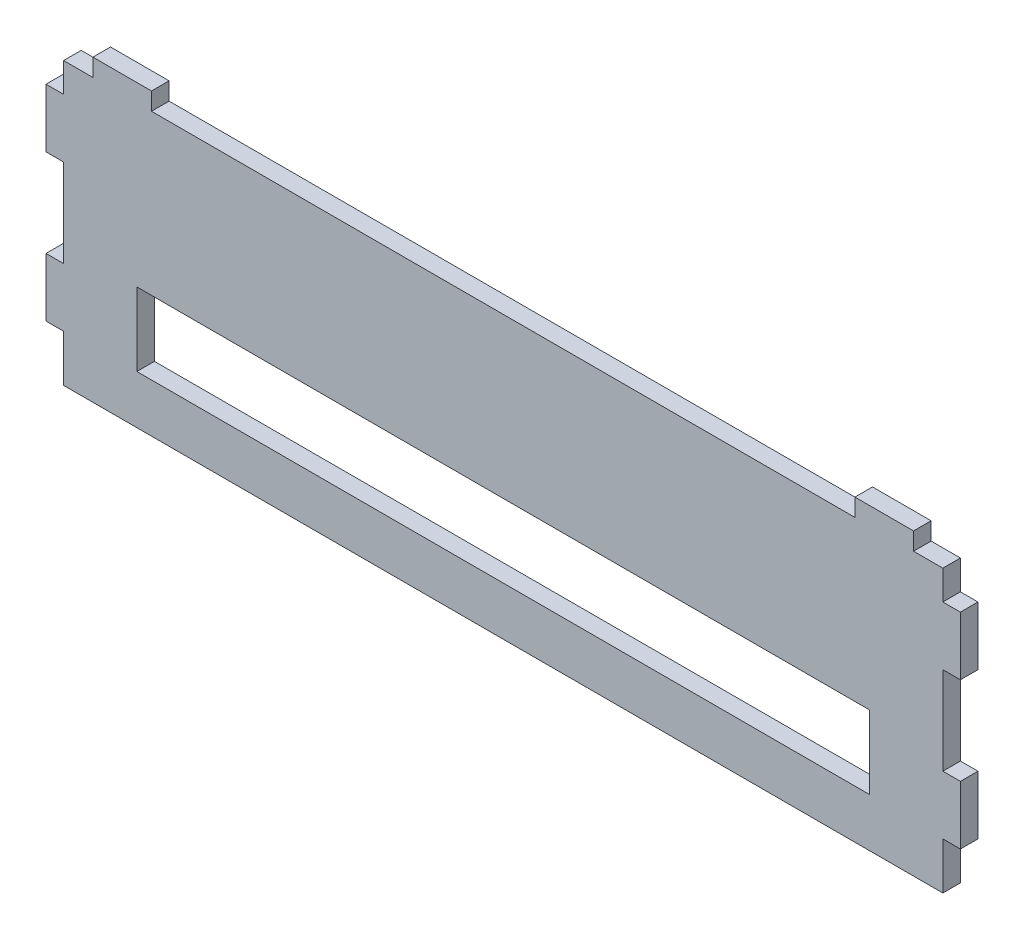
SolidWorks part; units mm, degrees
ref_plane "Front Plane" through (0, 0, 0) normal (0, 0, 1) x (1, 0, 0)
ref_plane "Top Plane" through (0, 0, 0) normal (0, 1, 0) x (1, 0, 0)
ref_plane "Right Plane" through (0, 0, 0) normal (1, 0, 0) x (0, 0, -1)
sketch "Sketch1" plane through (0, 0, 0) normal (0, 0, 1) x (1, 0, 0)
  line L0 (495.5689, -96) -> (195.5689, -96)
  line L1 (495.5689, 0) -> (485.5689, 0)
  line L2 (495.5689, 0) -> (495.5689, -10)
  line L3 (495.5689, -102) -> (195.5689, -102) construction
  line L4 (195.5689, 0) -> (195.5689, -10)
  line L5 (195.5689, -102) -> (195.5689, -80) construction
  line L6 (501.5689, -80) -> (501.5689, -60) construction
  line L7 (501.5689, -60) -> (495.5689, -60) construction
  line L9 (495.5689, -80) -> (501.5689, -80) construction
  line L10 (501.5689, -30) -> (501.5689, -10) construction
  line L11 (501.5689, -10) -> (495.5689, -10) construction
  line L13 (495.5689, -30) -> (501.5689, -30) construction
  line L15 (485.5689, 0) -> (485.5689, 6) construction
  line L16 (485.5689, 6) -> (465.5689, 6) construction
  line L17 (465.5689, 6) -> (465.5689, 0) construction
  line L18 (225.5689, 6) -> (205.5689, 6) construction
  line L19 (205.5689, 6) -> (205.5689, 0) construction
  line L21 (225.5689, 0) -> (225.5689, 6) construction
  line L23 (195.5689, -10) -> (189.5689, -10) construction
  line L24 (189.5689, -10) -> (189.5689, -30) construction
  line L25 (189.5689, -30) -> (195.5689, -30) construction
  line L27 (195.5689, -60) -> (189.5689, -60) construction
  line L28 (189.5689, -60) -> (189.5689, -80) construction
  line L29 (189.5689, -80) -> (195.5689, -80) construction
  line L30 (501.5689, -80) -> (501.5689, -60)
  line L31 (501.5689, -60) -> (495.5689, -60)
  line L33 (495.5689, -80) -> (501.5689, -80)
  line L34 (501.5689, -30) -> (501.5689, -10)
  line L35 (501.5689, -10) -> (495.5689, -10)
  line L37 (495.5689, -30) -> (501.5689, -30)
  line L39 (485.5689, 0) -> (485.5689, 6)
  line L40 (485.5689, 6) -> (465.5689, 6)
  line L41 (465.5689, 6) -> (465.5689, 0)
  line L42 (225.5689, 6) -> (205.5689, 6)
  line L43 (205.5689, 6) -> (205.5689, 0)
  line L45 (225.5689, 0) -> (225.5689, 6)
  line L47 (195.5689, -10) -> (189.5689, -10)
  line L48 (189.5689, -10) -> (189.5689, -30)
  line L49 (189.5689, -30) -> (195.5689, -30)
  line L51 (195.5689, -60) -> (189.5689, -60)
  line L52 (189.5689, -60) -> (189.5689, -80)
  line L53 (189.5689, -80) -> (195.5689, -80)
  line L54 (495.5689, -80) -> (495.5689, -96)
  line L55 (495.5689, -30) -> (495.5689, -60)
  line L56 (465.5689, 0) -> (225.5689, 0)
  line L57 (195.5689, -30) -> (195.5689, -60)
  line L58 (205.5689, 0) -> (195.5689, 0)
  line L59 (195.5689, -80) -> (195.5689, -96)
  line L60 (345.5689, -96) -> (345.5689, -79.4) construction
  line L61 (470.5689, -54.4) -> (220.5689, -54.4)
  line L62 (470.5689, -54.4) -> (470.5689, -79.4)
  line L63 (470.5689, -79.4) -> (220.5689, -79.4)
  line L64 (220.5689, -54.4) -> (220.5689, -79.4)
  line L65 (450.5689, -69.4) -> (240.5689, -69.4) construction
  line L66 (450.5689, -69.4) -> (240.5689, -69.4) construction
  dimension "D1" = 6
  dimension "D2" = 20
  dimension "D3" = 10
  dimension "D4" = 15
extrude "Boss-Extrude1" add sketch "Sketch1" against normal up to surface (6 mm away)
